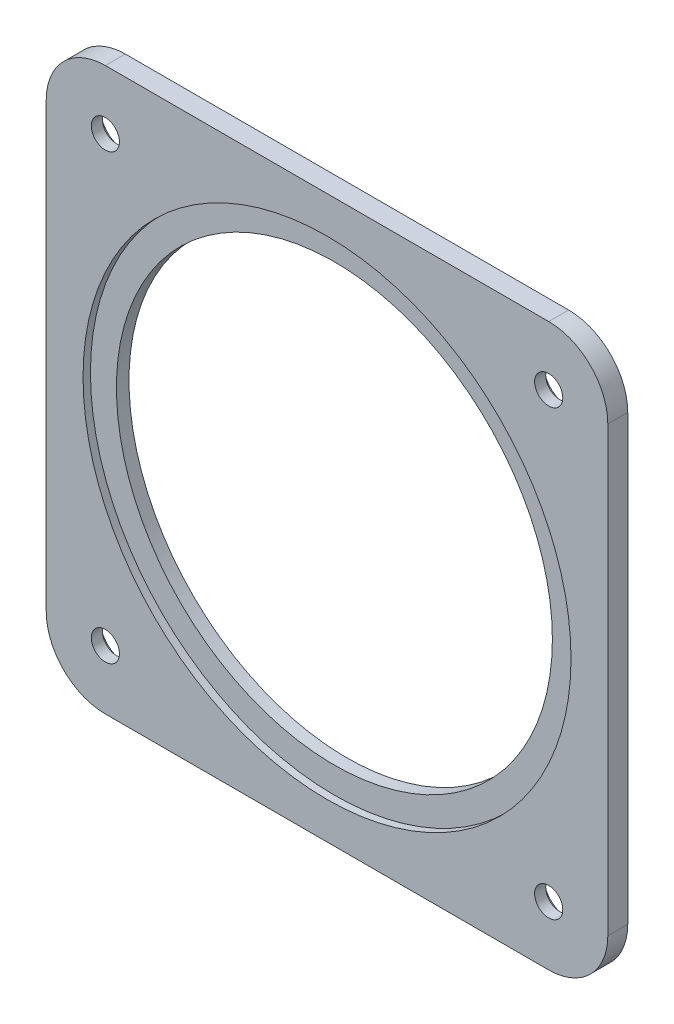
SolidWorks part; units mm, degrees
ref_plane "Front Plane" through (0, 0, 0) normal (0, 0, 1) x (1, 0, 0)
ref_plane "Top Plane" through (0, 0, 0) normal (0, 1, 0) x (1, 0, 0)
ref_plane "Right Plane" through (0, 0, 0) normal (1, 0, 0) x (0, 0, -1)
sketch "Sketch1" plane through (0, 0, 0) normal (0, 0, 1) x (1, 0, 0)
  line L1 (75, -95) -> (-75, -95)
  line L2 (95, -75) -> (95, 75)
  line L3 (75, 95) -> (-75, 95)
  line L4 (-95, -75) -> (-95, 75)
  line L5 (95, -95) -> (-95, 95) construction
  line L6 (95, 95) -> (-95, -95) construction
  arc A0 (-75, -95) -> (-95, -75) centre (-75, -75) cw
  arc A1 (75, -95) -> (95, -75) centre (75, -75) ccw
  arc A2 (95, 75) -> (75, 95) centre (75, 75) ccw
  arc A3 (-75, 95) -> (-95, 75) centre (-75, 75) ccw
  circle A4 centre (0, 0) radius 73.75
  circle A5 centre (-75, 75) radius 4.7625
  circle A9 centre (75, 75) radius 4.7625
  circle A10 centre (75, -75) radius 4.7625
  circle A11 centre (-75, -75) radius 4.7625
  point P0 (0, 0)
  point P31 (0, 0)
  point P32 (0, 0)
  dimension "D3" = 20
  dimension "D4" = 147.5
  dimension "D6" = 9.525
  dimension "D1" = 190
  dimension "D2" = 190
  dimension "D5" = 20
  dimension "D7" = 4
extrude "Boss-Extrude1" add sketch "Sketch1" along normal blind 6.75
sketch "Sketch2" plane through (0, 0, 0) normal (0, 0, -1) x (-1, 0, 0)
  line L0 (95, 75) -> (95, -75) construction
  line L1 (-75, 95) -> (75, 95) construction
  circle A0 centre (-75, 75) radius 8.5
  circle A4 centre (75, 75) radius 8.5
  circle A5 centre (75, -75) radius 8.5
  circle A6 centre (-75, -75) radius 8.5
  point P12 (1.3909, -1.3909)
  point P17 (0, 0)
  dimension "D1" = 17
  dimension "D3" = 170
  dimension "D4" = 20
  dimension "D2" = 4
extrude "Cut-Extrude1" cut sketch "Sketch2" against normal blind 3
sketch "Sketch3" plane through (0, 0, 6.75) normal (0, 0, 1) x (1, 0, 0)
  circle A0 centre (0, 0) radius 82.55
  dimension "D1" = 165.1
extrude "Cut-Extrude2" cut sketch "Sketch3" against normal blind 2.5
